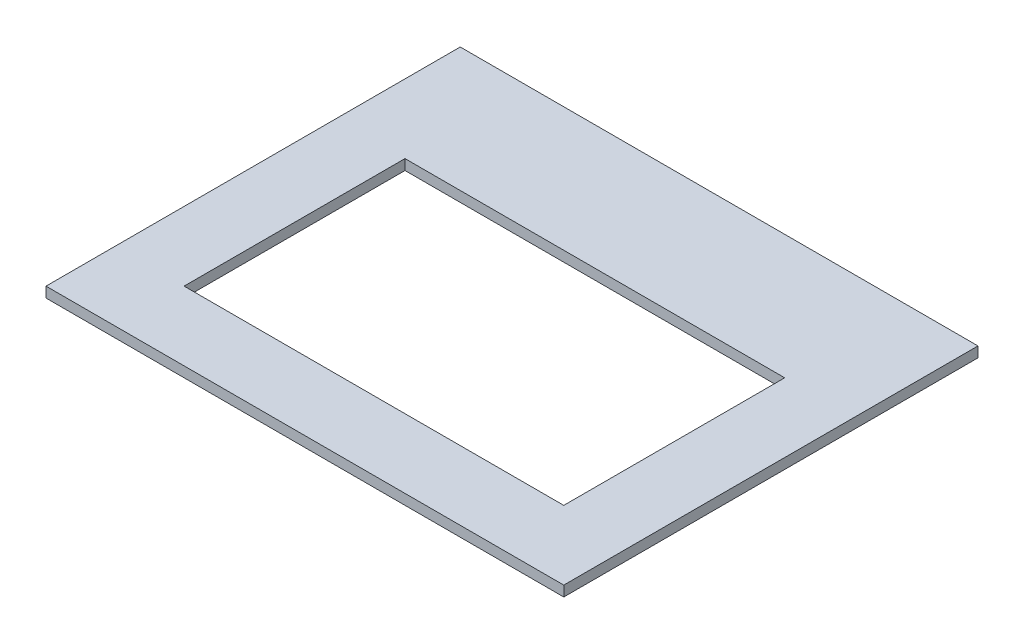
SolidWorks part; units mm, degrees
ref_plane "前视基准面" through (0, 0, 0) normal (0, 0, 1) x (1, 0, 0)
ref_plane "上视基准面" through (0, 0, 0) normal (0, 1, 0) x (1, 0, 0)
ref_plane "右视基准面" through (0, 0, 0) normal (1, 0, 0) x (0, 0, -1)
sketch "草图1" plane through (0, 0, 0) normal (0, 1, 0) x (1, 0, 0)
  line L0 (0, 0) -> (150, 0)
  line L1 (150, 0) -> (150, -120)
  line L2 (150, -120) -> (0, -120)
  line L3 (0, -120) -> (0, 0)
extrude "凸台-拉伸1" add sketch "草图1" along normal blind 3
sketch "草图2" plane through (0, 0, 0) normal (0, -1, 0) x (1, 0, 0)
  line L0 (20, 100) -> (130, 100)
  line L1 (130, 100) -> (130, 36)
  line L4 (20, 100) -> (20, 36)
  line L5 (20, 36) -> (130, 36)
  line L6 (150, 0) -> (0, 0) construction
  line L7 (0, 0) -> (0, 120) construction
  line L8 (0, 120) -> (150, 120) construction
  line L9 (150, 120) -> (150, 0) construction
  dimension "D1" = 36
  dimension "D2" = 20
  dimension "D3" = 20
  dimension "D4" = 20
extrude "切除-拉伸1" cut sketch "草图2" against normal blind 3 contours L5 L1 L0 L4
